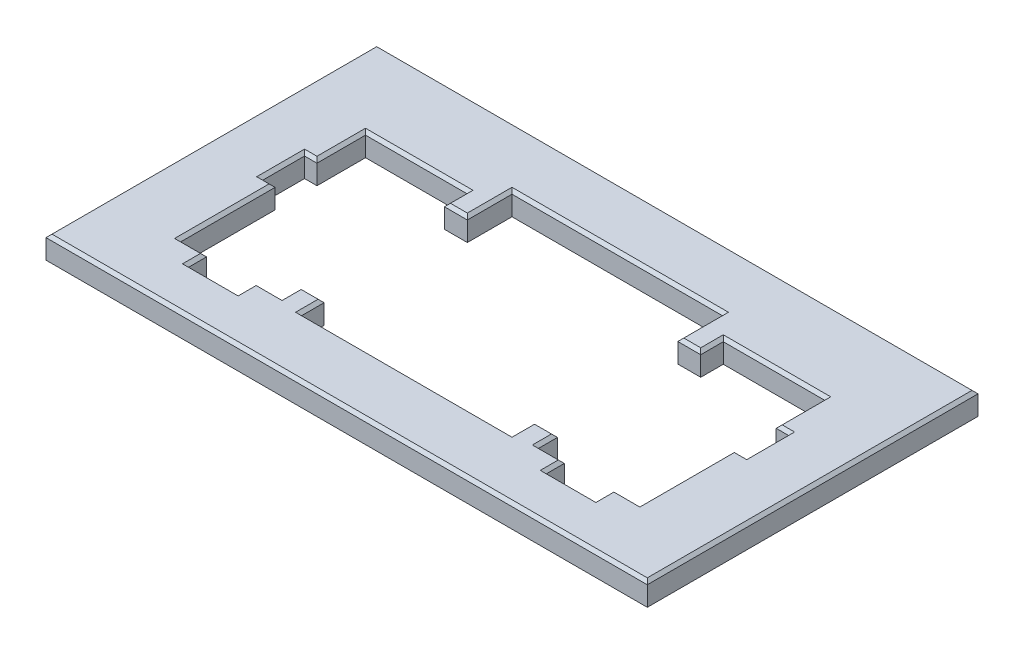
SolidWorks part; units mm, degrees
ref_plane "Front Plane" through (0, 0, 0) normal (0, 0, 1) x (1, 0, 0)
ref_plane "Top Plane" through (0, 0, 0) normal (0, 1, 0) x (1, 0, 0)
ref_plane "Right Plane" through (0, 0, 0) normal (1, 0, 0) x (0, 0, -1)
sketch "Sketch1" plane through (0, 0, 0) normal (0, 1, 0) x (1, 0, 0)
  line L1 (-20, 11) -> (20, 11)
  line L2 (-20, 11) -> (-20, -11)
  line L3 (-20, -11) -> (20, -11)
  line L4 (20, 11) -> (20, -11)
  line L5 (-20, 11) -> (20, -11) construction
  line L6 (-20, -11) -> (20, 11) construction
  point P0 (0, 0)
  dimension "D1" = 40
  dimension "D2" = 22
extrude "Boss-Extrude1" add sketch "Sketch1" along normal blind 1.5
sketch "Sketch2" plane through (0, 1.5, 0) normal (0, 1, 0) x (1, 0, 0)
  line L0 (-7, 4.03) -> (-8.525, 4.03)
  line L1 (-7, 7) -> (7, 7)
  line L2 (-7, 7) -> (-7, 4.03)
  line L3 (-7, -7) -> (7, -7)
  line L4 (7, 7) -> (7, 4.03)
  line L5 (-7, 7) -> (7, -7) construction
  line L6 (-7, -7) -> (7, 7) construction
  line L7 (-8.525, 4.03) -> (-8.525, 5.53)
  line L8 (-8.525, 5.53) -> (-15.275, 5.53)
  line L9 (-15.275, 5.53) -> (-15.275, 2.3)
  line L10 (-15.275, 2.3) -> (-16.1, 2.3)
  line L11 (-16.1, 2.3) -> (-16.1, -0.485)
  line L12 (-16.1, -0.485) -> (-15.275, -0.485)
  line L13 (-15.275, -0.485) -> (-15.275, -6.77)
  line L14 (-15.275, -6.77) -> (-13.55, -6.77)
  line L15 (-13.55, -6.77) -> (-13.55, -7.97)
  line L16 (-13.55, -7.97) -> (-10.25, -7.97)
  line L17 (-10.25, -7.97) -> (-10.25, -6.77)
  line L18 (-10.25, -6.77) -> (-8.525, -6.77)
  line L19 (-8.525, -6.77) -> (-8.525, -5.5)
  line L20 (-8.525, -5.5) -> (-7, -5.5)
  line L21 (-11.9, -7.97) -> (-11.9, -2.5905) construction
  line L22 (0, 0) -> (0, 7) construction
  line L23 (11.9, -7.97) -> (11.9, -2.5905) construction
  line L24 (8.525, -5.5) -> (7, -5.5)
  line L25 (8.525, -6.77) -> (8.525, -5.5)
  line L26 (10.25, -6.77) -> (8.525, -6.77)
  line L27 (10.25, -7.97) -> (10.25, -6.77)
  line L28 (13.55, -7.97) -> (10.25, -7.97)
  line L29 (13.55, -6.77) -> (13.55, -7.97)
  line L30 (15.275, -6.77) -> (13.55, -6.77)
  line L31 (15.275, -0.485) -> (15.275, -6.77)
  line L32 (16.1, -0.485) -> (15.275, -0.485)
  line L33 (16.1, 2.3) -> (16.1, -0.485)
  line L34 (15.275, 2.3) -> (16.1, 2.3)
  line L35 (15.275, 5.53) -> (15.275, 2.3)
  line L36 (8.525, 5.53) -> (15.275, 5.53)
  line L37 (8.525, 4.03) -> (8.525, 5.53)
  line L38 (7, 4.03) -> (8.525, 4.03)
  line L39 (-7, -5.5) -> (-7, -7)
  line L40 (7, -5.5) -> (7, -7)
  point P0 (0, 0)
  dimension "D1" = 14
  dimension "D2" = 14
  dimension "D3" = 1.525
  dimension "D4" = 1.5
  dimension "D5" = 6.75
  dimension "D6" = 3.23
  dimension "D7" = 2.785
  dimension "D8" = 0.825
  dimension "D9" = 6.285
  dimension "D10" = 3.3
  dimension "D11" = 1.725
  dimension "D12" = 1.5
  dimension "D13" = 1.27
  dimension "D14" = 1.2
extrude "Cut-Extrude1" cut sketch "Sketch2" against normal through all
chamfer "Chamfer1" distance 0.2 angle 45 40 edges at (0, 1.5, 11) (-20, 1.5, 0) (0, 1.5, -11) (20, 1.5, 0) (7.7625, 1.5, 5.5) (8.525, 1.5, 6.135) (9.3875, 1.5, 6.77) (10.25, 1.5, 7.37) (11.9, 1.5, 7.97) (13.55, 1.5, 7.37) (14.4125, 1.5, 6.77) (15.275, 1.5, 3.6275) (15.6875, 1.5, 0.485) (16.1, 1.5, -0.9075) (15.6875, 1.5, -2.3) (15.275, 1.5, -3.915) (11.9, 1.5, -5.53) (8.525, 1.5, -4.78) (7.7625, 1.5, -4.03) (7, 1.5, -5.515) (0, 1.5, -7) (-7, 1.5, -5.515) (-7.7625, 1.5, -4.03) (-8.525, 1.5, -4.78) (-11.9, 1.5, -5.53) (-15.275, 1.5, -3.915) (-15.6875, 1.5, -2.3) (-16.1, 1.5, -0.9075) (-15.6875, 1.5, 0.485) (-15.275, 1.5, 3.6275) (-14.4125, 1.5, 6.77) (-13.55, 1.5, 7.37) (-11.9, 1.5, 7.97) (-10.25, 1.5, 7.37) (-9.3875, 1.5, 6.77) (-8.525, 1.5, 6.135) (-7.7625, 1.5, 5.5) (-7, 1.5, 6.25) (0, 1.5, 7) (7, 1.5, 6.25)
